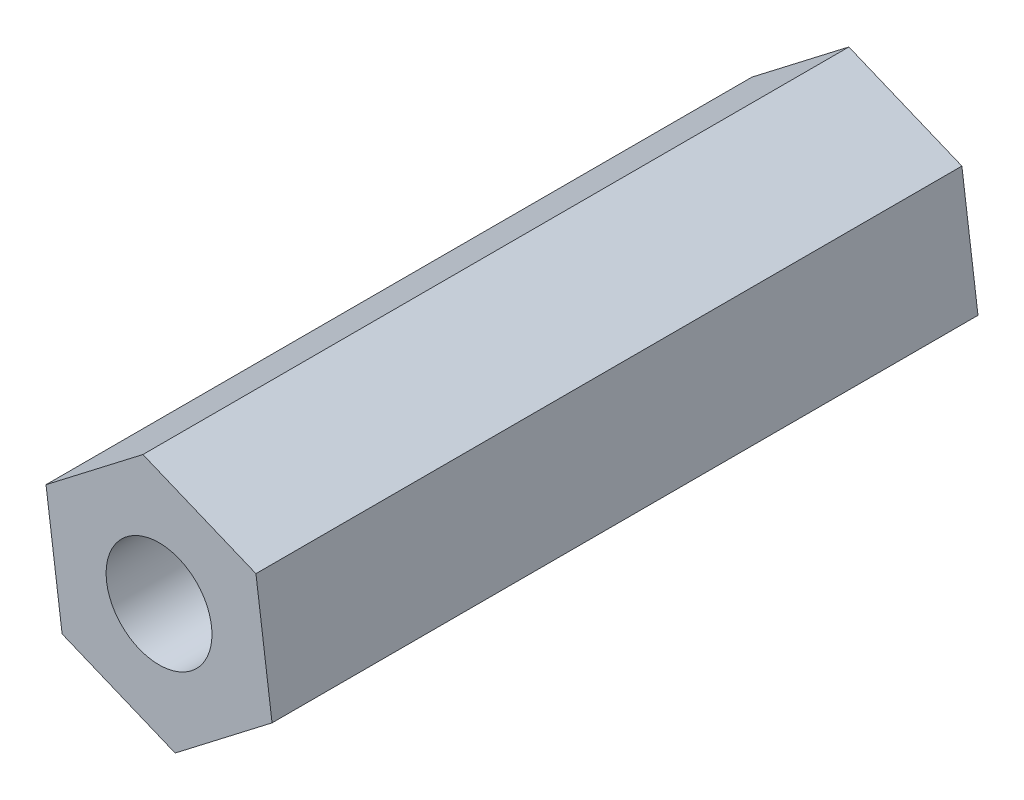
SolidWorks part; units mm, degrees
material "ABS"
ref_plane "Plano frontal" through (0, 0, 0) normal (0, 0, 1) x (1, 0, 0)
ref_plane "Plano superior" through (0, 0, 0) normal (0, 1, 0) x (1, 0, 0)
ref_plane "Plano direito" through (0, 0, 0) normal (1, 0, 0) x (0, 0, -1)
sketch "Esboço1" plane through (0, 0, 0) normal (0, 0, 1) x (1, 0, 0)
  line L1 (8.7339, -0.991) -> (5.5317, 0.3304)
  line L2 (5.5317, 0.3304) -> (2.7862, -1.782)
  line L3 (2.7862, -1.782) -> (3.2429, -5.2159)
  line L4 (3.2429, -5.2159) -> (6.4451, -6.5373)
  line L5 (6.4451, -6.5373) -> (9.1906, -4.4249)
  line L6 (9.1906, -4.4249) -> (8.7339, -0.991)
  circle A0 centre (5.9884, -3.1034) radius 3 construction
extrude "Ressalto-extrusão1" add sketch "Esboço1" along normal blind 20
sketch "Esboço2" plane through (0, 0, 0) normal (0, 0, -1) x (-1, 0, 0)
  line L0 (-9.1906, -4.4249) -> (-8.7339, -0.991) construction
  circle A0 centre (-5.9883, -3.1025) radius 1.5
  dimension "D1" = 3
  dimension "D2" = 3.465
  dimension "D3" = 3
extrude "Corte-extrusão1" cut sketch "Esboço2" against normal blind 20
